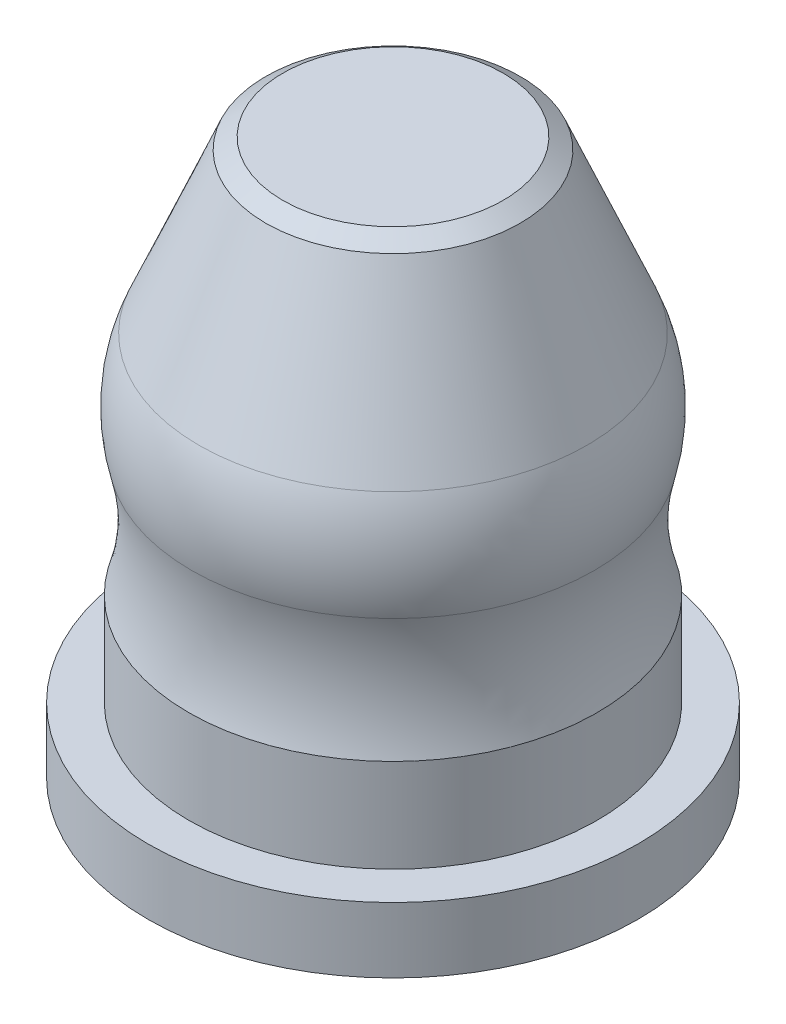
SolidWorks part; units mm, degrees
ref_plane "Front Plane" through (0, 0, 0) normal (0, 0, 1) x (1, 0, 0)
ref_plane "Top Plane" through (0, 0, 0) normal (0, 1, 0) x (1, 0, 0)
ref_plane "Right Plane" through (0, 0, 0) normal (1, 0, 0) x (0, 0, -1)
sketch "Sketch1" plane through (0, 0, 0) normal (0, 0, 1) x (1, 0, 0)
  line L0 (0, 0) -> (0, -22758.8018) construction
  line L1 (0, 0) -> (25, 0)
  line L2 (0, 0) -> (0, 60)
  line L3 (0, 60) -> (13.5, 60)
  line L4 (15.5812, 58.6172) -> (23.7609, 39.1575)
  line L5 (25, 0) -> (25, 11.4238)
  line L6 (13.5, 60) -> (15.5812, 58.6172)
  arc A0 (23.7609, 39.1575) -> (24.6723, 26.3457) centre (5.3235, 31.4076) cw
  arc A1 (25, 11.4238) -> (24.6723, 26.3457) centre (50.9955, 19.4592) cw
  point P11 (15, 60)
  dimension "D5" = 20
  dimension "D9" = 50.9955
  dimension "D1" = 25
  dimension "D2" = 60
  dimension "D3" = 15
  dimension "D10" = 5.3235
revolve "Revolve1" add sketch "Sketch1" angle 360 about L0
sketch "Sketch2" plane through (0, 0, 0) normal (0, -1, 0) x (1, 0, 0)
  circle A0 centre (0, 0) radius 30
  dimension "D1" = 60
extrude "Boss-Extrude1" add sketch "Sketch2" along normal blind 8
